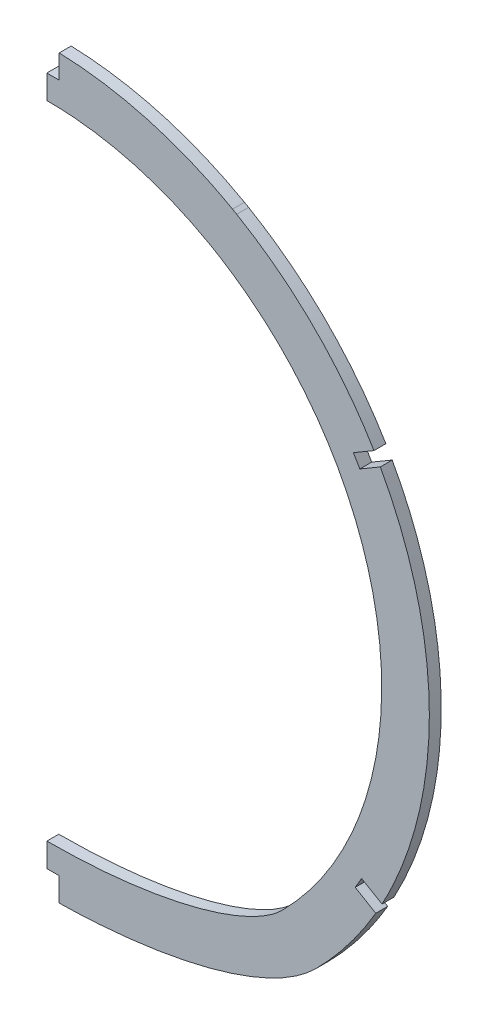
SolidWorks part; units mm, degrees
material "Plywood"
ref_plane "Front Plane" through (0, 0, 0) normal (0, 0, 1) x (1, 0, 0)
ref_plane "Top Plane" through (0, 0, 0) normal (0, 1, 0) x (1, 0, 0)
ref_plane "Right Plane" through (0, 0, 0) normal (1, 0, 0) x (0, 0, -1)
sketch "Sketch2" plane through (0, 0, 0) normal (0, 0, 1) x (1, 0, 0)
  spline S0 degree 3 poles (2568.0953, -4090.4659) (-4057.024, 3451.1389) (4945.1528, -1980.2124) (-4825.8731, 402.3844) knots -545.10296 -545.10296 -545.10296 -545.10296 547.49362 547.49362 547.49362 547.49362 only from (49.5009, 91.348) to (50.6103, 90.7129)
  spline S1 degree 3 poles (3341.4723, -3725.6669) (-100.6677, -22.1088) (-50.1916, -95.8099) (-74.4696, -70.0026) (-75.8372, -68.488) (-77.1861, -66.9319) (-78.5157, -65.3347) (-79.8244, -63.6962) (-81.5476, -61.4464) (-83.6416, -58.5297) (-85.6296, -55.5014) (-87.1622, -52.9973) (-88.2859, -51.0701) (-90.1147, -47.7724) (-92.5499, -42.8914) (-95.3516, -36.1752) (-97.8068, -28.8548) (-99.4166, -22.4927) (-100.4844, -16.9735) (-101.2174, -12.1158) (-101.8059, -6.1085) (-102.0556, 1.0556) (-101.6376, 11.9166) (-99.5817, 24.7034) (-94.9478, 39.4776) (-88.6565, 52.7081) (-80.0434, 65.5541) (-69.8712, 76.7554) (-58.637, 85.9148) (-47.202, 92.899) (-35.7905, 98.0522) (-24.0008, 101.7167) (-12.0295, 103.8942) (-3.6569, 104.3953) (0.9911, 104.3723) (2.6447, 104.3478) (5.2959, 104.2559) (8.9441, 104.0024) (12.9235, 103.5662) (16.8979, 102.9692) (20.8607, 102.2106) (24.805, 101.2899) (28.7242, 100.207) (32.6113, 98.9619) (36.4593, 97.5551) (39.9429, 96.1186) (42.4433, 94.9816) (43.9946, 94.2376) (44.9225, 93.7809) (45.8466, 93.3143) (46.7667, 92.8378) (47.6827, 92.3514) (70.4007, 80.003) (151.5153, 23.3747) (-4363.3748, 2440.7113) knots -0.313173 -0.313173 -0.313173 -0.313173 0.006795 0.013654 0.020575 0.02756 0.034609 0.041722 0.048899 0.063446 0.078252 0.085753 0.09332 0.100952 0.124124 0.148785 0.174948 0.202627 0.215494 0.232144 0.2526 0.276886 0.305032 0.363116 0.408011 0.462235 0.511576 0.564908 0.615598 0.658549 0.700916 0.742691 0.78387 0.82445 0.827809 0.831171 0.841279 0.854802 0.868378 0.882008 0.895692 0.909428 0.923217 0.93706 0.950955 0.964902 0.975398 0.978902 0.982411 0.985922 0.989437 0.992954 0.996476 1.262403 1.262403 1.262403 1.262403 only from (-71.6774, -72.9104) to (49.5009, 91.348)
  spline S2 degree 3 poles (-71.6774, -72.9104) (-72.1092, -72.4767) (-72.9729, -71.5936) (-74.4696, -70.0026) (-75.8372, -68.488) (-77.1861, -66.9319) (-78.5157, -65.3347) (-79.8244, -63.6962) (-81.5476, -61.4464) (-83.6416, -58.5297) (-85.6296, -55.5014) (-87.1622, -52.9973) (-88.2859, -51.0701) (-90.1147, -47.7724) (-92.5499, -42.8914) (-95.3516, -36.1752) (-97.8068, -28.8548) (-99.4166, -22.4927) (-100.4844, -16.9735) (-101.2174, -12.1158) (-101.8059, -6.1085) (-102.0556, 1.0556) (-101.6376, 11.9166) (-99.5817, 24.7034) (-94.9478, 39.4776) (-88.6565, 52.7081) (-80.0434, 65.5541) (-69.8712, 76.7554) (-58.637, 85.9148) (-47.202, 92.899) (-35.7905, 98.0522) (-24.0008, 101.7167) (-12.0295, 103.8942) (-3.6569, 104.3953) (0.9911, 104.3723) (2.6447, 104.3478) (5.2959, 104.2559) (8.9441, 104.0024) (12.9235, 103.5662) (16.8979, 102.9692) (20.8607, 102.2106) (24.805, 101.2899) (28.7242, 100.207) (32.6113, 98.9619) (36.4593, 97.5551) (39.9429, 96.1186) (42.4433, 94.9816) (43.9946, 94.2376) (44.9225, 93.7809) (45.8466, 93.3143) (46.7667, 92.8378) (47.6827, 92.3514) (48.5618, 91.8735) (49.1883, 91.5244) (49.5009, 91.348) knots 0 0 0 0 0.006795 0.013654 0.020575 0.02756 0.034609 0.041722 0.048899 0.063446 0.078252 0.085753 0.09332 0.100952 0.124124 0.148785 0.174948 0.202627 0.215494 0.232144 0.2526 0.276886 0.305032 0.363116 0.408011 0.462235 0.511576 0.564908 0.615598 0.658549 0.700916 0.742691 0.78387 0.82445 0.827809 0.831171 0.841279 0.854802 0.868378 0.882008 0.895692 0.909428 0.923217 0.93706 0.950955 0.964902 0.975398 0.978902 0.982411 0.985922 0.989437 0.992954 0.996476 1 1 1 1
  spline S3 degree 3 poles (49.5009, 91.348) (49.872, 91.1385) (50.2418, 90.9268) (50.6103, 90.7129) knots 0 0 0 0 1 1 1 1
  spline S4 degree 3 poles (-4193.7763, 2732.8048) (81.5381, 53.7028) (23.1515, 107.7521) (53.9325, 88.7036) (55.5798, 87.6387) (57.2181, 86.5331) (58.847, 85.3874) (60.4652, 84.2011) (62.6149, 82.559) (65.2687, 80.4032) (68.3802, 77.661) (71.4204, 74.7537) (74.3792, 71.6812) (77.2464, 68.4441) (79.5428, 65.6199) (81.3243, 63.2803) (82.6352, 61.4798) (83.9151, 59.6395) (85.6826, 56.9767) (87.8969, 53.3695) (90.4626, 48.6769) (92.8892, 43.6261) (95.1327, 38.2157) (97.1465, 32.4482) (98.8821, 26.3306) (100.2892, 19.8751) (101.2586, 13.4739) (101.8173, 7.2467) (102.0152, 1.305) (101.8786, -4.6242) (101.3926, -10.7347) (100.5371, -16.8676) (99.3294, -22.8638) (97.8936, -28.3722) (96.657, -32.2698) (95.7856, -34.7444) (95.046, -36.7643) (93.9532, -39.5358) (92.4358, -43.007) (90.8217, -46.3649) (89.1186, -49.6082) (87.3342, -52.7363) (85.4757, -55.7486) (83.5505, -58.6453) (81.5655, -61.4266) (79.3077, -64.3807) (77.437, -66.6472) (76.0073, -68.2889) (75.2951, -69.0897) (74.579, -69.8782) (73.8594, -70.6545) (73.1363, -71.4184) (59.0939, -85.9325) (120.7935, -16.6257) (-3396.6628, -3673.2191) knots -0.504739 -0.504739 -0.504739 -0.504739 0.010157 0.020393 0.030709 0.041103 0.051576 0.062128 0.072758 0.094254 0.116062 0.138181 0.16061 0.183347 0.206391 0.218027 0.22974 0.241529 0.253393 0.280162 0.30828 0.337739 0.36853 0.400644 0.434071 0.4688 0.504821 0.536145 0.567394 0.59857 0.62967 0.664059 0.696204 0.726123 0.75383 0.760691 0.767516 0.787768 0.807688 0.827278 0.84654 0.865477 0.884089 0.902378 0.920346 0.937994 0.961032 0.966703 0.97234 0.977942 0.983508 0.98904 0.994538 1.266327 1.266327 1.266327 1.266327 only from (50.6103, 90.7129) to (71.6784, -72.9104)
  spline S5 degree 3 poles (50.6103, 90.7129) (51.1284, 90.4118) (52.1672, 89.796) (53.9325, 88.7036) (55.5798, 87.6387) (57.2181, 86.5331) (58.847, 85.3874) (60.4652, 84.2011) (62.6149, 82.559) (65.2687, 80.4032) (68.3802, 77.661) (71.4204, 74.7537) (74.3792, 71.6812) (77.2464, 68.4441) (79.5428, 65.6199) (81.3243, 63.2803) (82.6352, 61.4798) (83.9151, 59.6395) (85.6826, 56.9767) (87.8969, 53.3695) (90.4626, 48.6769) (92.8892, 43.6261) (95.1327, 38.2157) (97.1465, 32.4482) (98.8821, 26.3306) (100.2892, 19.8751) (101.2586, 13.4739) (101.8173, 7.2467) (102.0152, 1.305) (101.8786, -4.6242) (101.3926, -10.7347) (100.5371, -16.8676) (99.3294, -22.8638) (97.8936, -28.3722) (96.657, -32.2698) (95.7856, -34.7444) (95.046, -36.7643) (93.9532, -39.5358) (92.4358, -43.007) (90.8217, -46.3649) (89.1186, -49.6082) (87.3342, -52.7363) (85.4757, -55.7486) (83.5505, -58.6453) (81.5655, -61.4266) (79.3077, -64.3807) (77.437, -66.6472) (76.0073, -68.2889) (75.2951, -69.0897) (74.579, -69.8782) (73.8594, -70.6545) (73.1363, -71.4184) (72.3175, -72.2647) (71.8912, -72.6967) (71.6784, -72.9104) knots 0 0 0 0 0.010157 0.020393 0.030709 0.041103 0.051576 0.062128 0.072758 0.094254 0.116062 0.138181 0.16061 0.183347 0.206391 0.218027 0.22974 0.241529 0.253393 0.280162 0.30828 0.337739 0.36853 0.400644 0.434071 0.4688 0.504821 0.536145 0.567394 0.59857 0.62967 0.664059 0.696204 0.726123 0.75383 0.760691 0.767516 0.787768 0.807688 0.827278 0.84654 0.865477 0.884089 0.902378 0.920346 0.937994 0.961032 0.966703 0.97234 0.977942 0.983508 0.98904 0.994538 1 1 1 1
  spline S6 degree 3 poles (-4835.9061, 806.008) (5645.7753, -391.3089) (-5645.7177, -391.3145) (4835.7602, 805.9912) knots -2.930767 -2.930767 -2.930767 -2.930767 3.930735 3.930735 3.930735 3.930735 weights 1 1 1 1 only from (71.6784, -72.9104) to (-71.6774, -72.9104)
  spline S7 degree 3 poles (71.6784, -72.9104) (46.3599, -98.3417) (-46.3589, -98.3417) (-71.6774, -72.9104) knots 0 0 0 0 1 1 1 1 weights 1 1 1 1
  spline S8 degree 1 poles (-62.6772, -63.9502) (43.2582, 80.2883) knots 0 0 1 1 construction
  spline S9 degree 1 poles (43.2582, 80.2883) (44.2327, 79.7303) knots 0 0 1 1 construction
  spline S10 degree 1 poles (44.2327, 79.7303) (62.6782, -63.9502) knots 0 0 1 1 construction
  spline S11 degree 1 poles (62.6782, -63.9502) (-62.6772, -63.9502) knots 0 0 1 1 construction
  spline S12 degree 3 poles (-62.6772, -63.9502) (-62.8955, -63.7309) (-63.3217, -63.2983) (-64.0021, -62.5921) (-64.7538, -61.7946) (-65.7039, -60.7646) (-66.8046, -59.5274) (-68.5568, -57.4681) (-70.6482, -54.8355) (-73.8114, -50.469) (-77.3945, -44.7561) (-82.3029, -35.1354) (-86.8108, -22.36) (-90.3543, -0.9674) (-87.6499, 26.3501) (-73.3334, 55.9721) (-49.624, 78.7088) (-24.4872, 89.3835) (-3.091, 92.1159) (13.039, 91.1975) (26.1203, 87.9966) (34.8794, 84.5248) (39.1021, 82.5104) (41.2143, 81.4108) (42.347, 80.7976) (42.9592, 80.4569) (43.2582, 80.2883) knots 0 0 0 0 0.003906 0.007812 0.011719 0.015625 0.023437 0.03125 0.046875 0.062499 0.093749 0.124999 0.187498 0.249998 0.374997 0.499996 0.624995 0.749994 0.812493 0.874993 0.937492 0.968742 0.984367 0.992179 0.996085 0.999992 0.999992 0.999992 0.999992
  spline S13 degree 3 poles (43.2582, 80.2883) (43.3397, 80.2423) (43.5025, 80.15) (43.7464, 80.0108) (43.9898, 79.871) (44.1518, 79.7773) (44.2327, 79.7303) knots 0.002022 0.002022 0.002022 0.002022 0.251014 0.500005 0.748996 0.997987 0.997987 0.997987 0.997987
  spline S14 degree 3 poles (44.2327, 79.7303) (44.5844, 79.526) (45.2596, 79.1276) (46.4154, 78.4223) (47.5738, 77.6928) (49.0079, 76.7584) (50.8048, 75.5306) (53.6072, 73.4932) (57.0034, 70.7903) (64.7641, 63.8421) (74.8536, 51.7693) (84.3118, 33.0007) (89.3026, 12.5818) (89.5941, -8.4639) (85.1673, -29.0225) (78.4712, -43.2887) (72.7378, -52.0045) (70.1455, -55.4923) (67.9548, -58.1887) (66.5372, -59.8344) (65.3768, -61.1241) (64.6361, -61.9238) (64.0489, -62.544) (63.5408, -63.0721) (63.0657, -63.5594) (62.8132, -63.8146) (62.6782, -63.9502) knots 0.000015 0.000015 0.000015 0.000015 0.007827 0.015639 0.023452 0.031264 0.046889 0.062514 0.093763 0.125013 0.250011 0.375009 0.500007 0.625005 0.750004 0.875002 0.906251 0.937501 0.953126 0.96875 0.976563 0.984375 0.988281 0.992188 0.996094 1 1 1 1
  spline S15 degree 3 poles (62.6782, -63.9502) (62.4421, -64.1873) (61.9735, -64.6322) (60.8483, -65.5949) (59.1789, -66.8259) (56.7375, -68.3252) (52.9423, -70.2888) (47.261, -72.5995) (39.2215, -74.978) (30.229, -76.8801) (17.3048, -78.7217) (0.0005, -79.6587) (-17.3038, -78.7217) (-30.228, -76.8801) (-39.2204, -74.978) (-47.2599, -72.5995) (-52.9413, -70.2888) (-56.7364, -68.3252) (-59.1779, -66.8259) (-60.8473, -65.5949) (-61.9724, -64.6322) (-62.4411, -64.1873) (-62.6772, -63.9502) knots 0 0 0 0 0.015625 0.03125 0.0625 0.09375 0.125 0.1875 0.25 0.3125 0.375 0.5 0.625 0.6875 0.75 0.8125 0.875 0.90625 0.9375 0.96875 0.984375 1 1 1 1
  dimension "D1" = 12.7
extrude "Boss-Extrude1" add sketch "Sketch2" against normal blind 3.175
sketch "Sketch3" plane through (0, 0, 0) normal (1, 0, 0) x (0, 0, -1)
  line L1 (-61.0107, 158.0584) -> (68.3789, 158.0584)
  line L2 (-61.0107, 158.0584) -> (-61.0107, -136.6623)
  line L3 (-61.0107, -136.6623) -> (68.3789, -136.6623)
  line L4 (68.3789, 158.0584) -> (68.3789, -136.6623)
extrude "Cut-Extrude1" cut sketch "Sketch3" against normal through all
sketch "Sketch4" plane through (0, 0, -3.175) normal (0, 0, -1) x (-1, 0, 0)
  line L0 (0, 0) -> (0, 91.6752) construction
  line L1 (0, 91.6752) -> (0, 98.0252) construction
  line L2 (-3.302, 98.0252) -> (3.302, 98.0252)
  line L3 (0, 98.0252) -> (0, 110.7252)
  line L4 (3.302, 98.0252) -> (3.302, 110.7252)
  line L5 (-3.302, 110.7252) -> (3.302, 110.7252)
  line L6 (77.1004, 46.575) -> (82.577, 49.789) construction
  line L7 (81.7221, 51.2458) -> (83.4319, 48.3323)
  line L8 (77.1004, 46.575) -> (0, 1.327) construction
  line L9 (81.7221, 51.2458) -> (92.6752, 57.6738)
  line L10 (83.4319, 48.3323) -> (94.385, 54.7603)
  line L11 (92.6752, 57.6738) -> (94.385, 54.7603)
  line L12 (77.572, -44.1978) -> (83.0486, -47.4118) construction
  line L13 (77.572, -44.1978) -> (0, 1.327) construction
  line L14 (82.1936, -48.8686) -> (83.9035, -45.955)
  line L15 (82.1936, -48.8686) -> (93.1467, -55.2966)
  line L16 (83.9035, -45.955) -> (94.8566, -52.3831)
  line L17 (93.1467, -55.2966) -> (94.8566, -52.3831)
  line L18 (0, 1.327) -> (0, -79.2839) construction
  line L19 (0, -79.2839) -> (0, -85.6339) construction
  line L20 (-3.302, -85.6339) -> (3.302, -85.6339)
  line L21 (0, -85.6339) -> (0, -98.3339)
  line L22 (3.302, -85.6339) -> (3.302, -98.3339)
  line L23 (-3.302, -98.3339) -> (3.302, -98.3339)
  line L24 (-77.572, -44.1978) -> (0, 1.327) construction
  line L25 (-77.572, -44.1978) -> (-83.0486, -47.4118) construction
  line L26 (-77.1004, 46.575) -> (0, 1.327) construction
  line L27 (-77.1004, 46.575) -> (-82.577, 49.789) construction
  line L28 (-3.302, -85.6339) -> (-3.302, -98.3339)
  line L29 (-93.1467, -55.2966) -> (-94.8566, -52.3831)
  line L30 (-83.9035, -45.955) -> (-94.8566, -52.3831)
  line L31 (-82.1936, -48.8686) -> (-93.1467, -55.2966)
  line L32 (-82.1936, -48.8686) -> (-83.9035, -45.955)
  line L33 (-92.6752, 57.6738) -> (-94.385, 54.7603)
  line L34 (-83.4319, 48.3323) -> (-94.385, 54.7603)
  line L35 (-81.7221, 51.2458) -> (-92.6752, 57.6738)
  line L36 (-81.7221, 51.2458) -> (-83.4319, 48.3323)
  line L37 (-3.302, 98.0252) -> (-3.302, 110.7252)
  point P15 (83.0486, -47.4118)
  dimension "D1" = 91.6752
  dimension "D2" = 6.35
  dimension "D3" = 3.302
  dimension "D4" = 12.7
  dimension "D5" = 59.593
  dimension "D6" = 1.327
  dimension "D7" = 89.3972
  dimension "D8" = 6.35
  dimension "D9" = 3.3782
  dimension "D10" = 12.7
  dimension "D11" = 59.593
  dimension "D12" = 89.944
  dimension "D13" = 6.35
  dimension "D14" = 3.3782
  dimension "D15" = 12.7
  dimension "D16" = 80.6109
  dimension "D17" = 6.35
  dimension "D18" = 3.302
  dimension "D19" = 12.7
extrude "Cut-Extrude2" cut sketch "Sketch4" against normal through all
